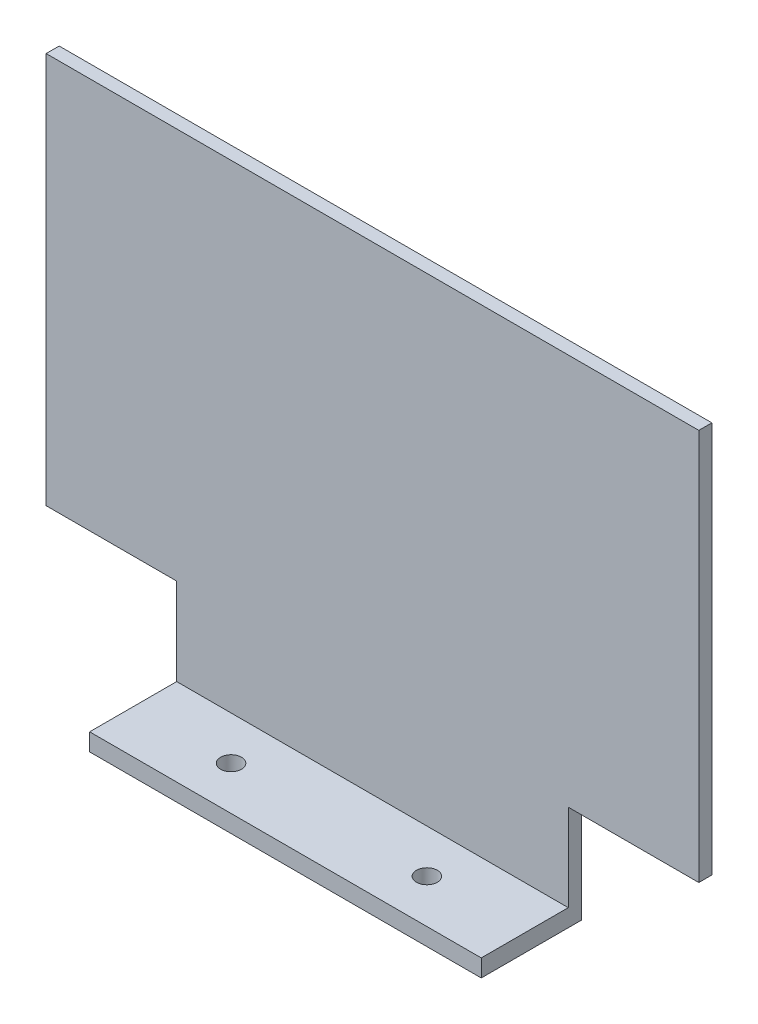
SolidWorks part; units mm, degrees
ref_plane "정면" through (0, 0, 0) normal (0, 0, 1) x (1, 0, 0)
ref_plane "윗면" through (0, 0, 0) normal (0, 1, 0) x (1, 0, 0)
ref_plane "우측면" through (0, 0, 0) normal (1, 0, 0) x (0, 0, -1)
sketch "스케치1" plane through (0, 0, 0) normal (0, 0, 1) x (1, 0, 0)
  line L1 (-75, 45) -> (75, 45)
  line L2 (-75, 45) -> (-75, -45)
  line L3 (-75, -45) -> (75, -45)
  line L4 (75, 45) -> (75, -45)
  line L5 (-75, 45) -> (75, -45) construction
  line L6 (-75, -45) -> (75, 45) construction
  point P4 (0, 0)
  point P5 (0, 0)
  dimension "D1" = 150
  dimension "D2" = 90
extrude "보스-돌출1" add sketch "스케치1" along normal blind 3 contours L1 L4 L3 L2
sketch "스케치2" plane through (0, 0, 0) normal (0, 0, 1) x (1, 0, 0)
  line L0 (-75, -45) -> (75, -45) construction
  line L1 (-45, -45) -> (45, -45)
  line L2 (-45, -45) -> (-45, -65)
  line L3 (-45, -65) -> (45, -65)
  line L4 (45, -45) -> (45, -65)
  line L5 (-45, -45) -> (45, -65) construction
  line L6 (-45, -65) -> (45, -45) construction
  point P4 (0, -55)
  point P7 (0, 0)
  dimension "D1" = 90
  dimension "D2" = 20
extrude "보스-돌출2" add sketch "스케치2" along normal blind 3
sketch "스케치3" plane through (0, 0, 0) normal (0, 0, 1) x (1, 0, 0)
  line L0 (45, -65) -> (45, -45) construction
  line L1 (-45, -65) -> (45, -65)
  line L2 (-45, -65) -> (-45, -69)
  line L3 (-45, -69) -> (45, -69)
  line L4 (45, -65) -> (45, -69)
  line L5 (-45, -65) -> (45, -69) construction
  line L6 (-45, -69) -> (45, -65) construction
  point P4 (0, -67)
  dimension "D1" = 4
extrude "보스-돌출3" add sketch "스케치3" along normal blind 23
sketch "스케치4" plane through (0, -69, 0) normal (0, -1, 0) x (1, 0, 0)
  line L0 (-45, 23) -> (45, 23) construction
  line L1 (-45, 0) -> (0, 0) construction
  line L2 (-45, 23) -> (-45, 0) construction
  line L3 (0, 0) -> (0, 23) construction
  circle A0 centre (-22.5, 13) radius 2.4
  circle A1 centre (22.5, 13) radius 2.4
  point P9 (-22.5, 0)
  dimension "D1" = 4.8
  dimension "D2" = 10
extrude "컷-돌출1" cut sketch "스케치4" against normal up to next
